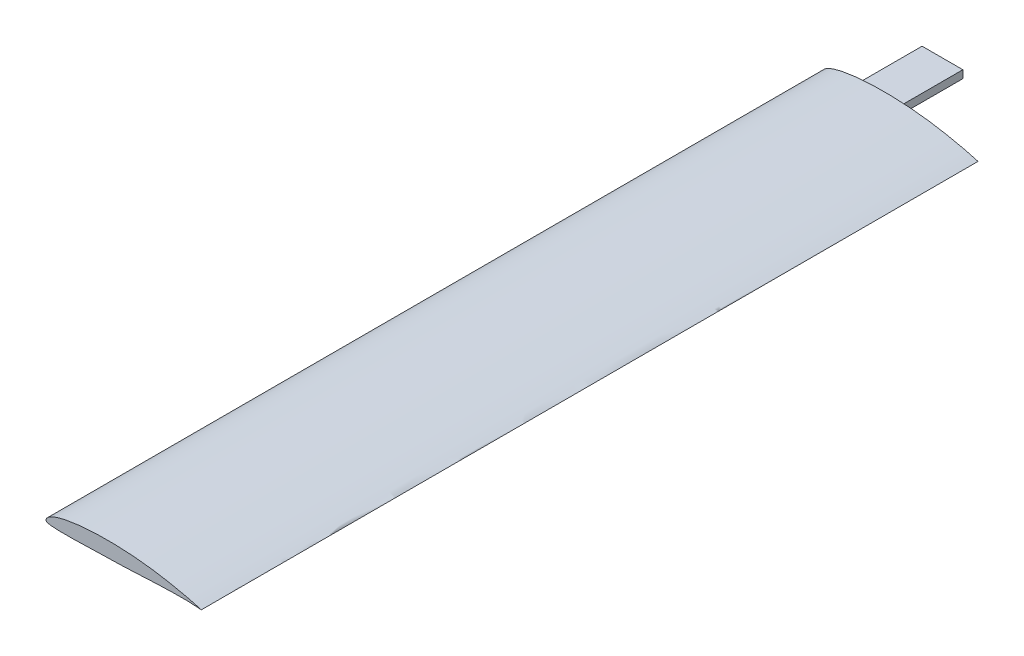
SolidWorks part; units mm, degrees
ref_plane "Front Plane" through (0, 0, 0) normal (0, 0, 1) x (1, 0, 0)
ref_plane "Top Plane" through (0, 0, 0) normal (0, 1, 0) x (1, 0, 0)
ref_plane "Right Plane" through (0, 0, 0) normal (1, 0, 0) x (0, 0, -1)
curve "Curve1"
  spline degree 3 poles (0.9957, 0.0006, 0) (1.0011, -0.0002, 0) (0.9959, 0.0009, 0) (0.992, 0.0022, 0) (0.9825, 0.005, 0) (0.9713, 0.0084, 0) (0.957, 0.0125, 0) (0.9402, 0.017, 0) (0.9208, 0.0217, 0) (0.8989, 0.0268, 0) (0.8748, 0.0321, 0) (0.8486, 0.0377, 0) (0.8205, 0.0435, 0) (0.7907, 0.0493, 0) (0.7596, 0.055, 0) (0.7273, 0.0605, 0) (0.6938, 0.0656, 0) (0.6594, 0.0702, 0) (0.6242, 0.0743, 0) (0.5883, 0.0778, 0) (0.552, 0.0808, 0) (0.5155, 0.0832, 0) (0.4788, 0.085, 0) (0.4423, 0.0861, 0) (0.4061, 0.0866, 0) (0.3705, 0.0865, 0) (0.3355, 0.0857, 0) (0.3015, 0.0843, 0) (0.2685, 0.0823, 0) (0.2368, 0.0797, 0) (0.2065, 0.0766, 0) (0.1779, 0.0729, 0) (0.151, 0.0687, 0) (0.126, 0.0641, 0) (0.1031, 0.059, 0) (0.0823, 0.0535, 0) (0.0638, 0.0477, 0) (0.0475, 0.0415, 0) (0.0337, 0.0351, 0) (0.0222, 0.0285, 0) (0.0131, 0.0217, 0) (0.0064, 0.0151, 0) (0.0018, 0.0085, 0) (0, 0.0023, 0) (-0.0004, -0.0036, 0) (0.0042, -0.0082, 0) (0.0115, -0.0108, 0) (0.0215, -0.0135, 0) (0.0347, -0.0154, 0) (0.0508, -0.0168, 0) (0.07, -0.0176, 0) (0.0921, -0.0181, 0) (0.117, -0.0183, 0) (0.1444, -0.0182, 0) (0.1743, -0.0179, 0) (0.2064, -0.0175, 0) (0.2404, -0.0168, 0) (0.2761, -0.016, 0) (0.3133, -0.0151, 0) (0.3517, -0.014, 0) (0.391, -0.0129, 0) (0.431, -0.0116, 0) (0.4715, -0.0102, 0) (0.5121, -0.0086, 0) (0.5527, -0.0067, 0) (0.5932, -0.0048, 0) (0.6332, -0.0027, 0) (0.6727, -0.0008, 0) (0.7112, 0.001, 0) (0.7485, 0.0026, 0) (0.7843, 0.0038, 0) (0.8183, 0.0047, 0) (0.8501, 0.0051, 0) (0.8795, 0.0053, 0) (0.9062, 0.005, 0) (0.9299, 0.0045, 0) (0.9504, 0.0037, 0) (0.9676, 0.0028, 0) (0.9807, 0.002, 0) (0.9914, 0.0009, 0) (0.9957, 0.0006, 0) (1.0011, -0.0002, 0) (0.9959, 0.0009, 0) knots -0.00876 -0.003931 -0.00099 0 0.000981 0.003818 0.008307 0.01426 0.021544 0.030087 0.039895 0.050943 0.063119 0.07632 0.090432 0.105336 0.120915 0.137032 0.153644 0.170716 0.188142 0.20585 0.223754 0.241763 0.259789 0.27774 0.295526 0.31306 0.33025 0.347009 0.363243 0.378876 0.393827 0.408018 0.421385 0.433867 0.445407 0.45597 0.465508 0.474013 0.481506 0.487961 0.493466 0.498109 0.501908 0.505061 0.50763 0.510153 0.5139 0.518982 0.525445 0.533392 0.54282 0.553698 0.565938 0.579453 0.594142 0.609906 0.626639 0.644212 0.662508 0.681404 0.700762 0.720455 0.740348 0.760327 0.780316 0.800229 0.819957 0.83938 0.858358 0.876742 0.89437 0.91109 0.926761 0.941228 0.954366 0.966044 0.976141 0.984569 0.99124 0.996069 0.99901 1 1.000981 1.003818 1.008307 periodic
sketch "Sketch1" plane through (0, 0, 0) normal (0, 0, 1) x (1, 0, 0)
  line L1 (20, 0) -> (0, 0) construction
  line L2 (0, 0) -> (0, 12.3044) construction
  spline S1 degree 3 poles (19.9149, 0.0124) (20.0212, -0.004) (19.9187, 0.0189) (19.8391, 0.0448) (19.6508, 0.0993) (19.4267, 0.1678) (19.1403, 0.251) (18.8046, 0.3407) (18.4164, 0.4352) (17.9794, 0.5368) (17.4964, 0.6443) (16.9719, 0.7563) (16.4102, 0.872) (15.8157, 0.9881) (15.1933, 1.1036) (14.5465, 1.2143) (13.8776, 1.3154) (13.1896, 1.4081) (12.4852, 1.4907) (11.7683, 1.5618) (11.0424, 1.6221) (10.3113, 1.6704) (9.5788, 1.7058) (8.8489, 1.7294) (8.1253, 1.7392) (7.412, 1.7372) (6.7128, 1.7222) (6.0317, 1.6945) (5.3723, 1.6553) (4.7384, 1.6044) (4.1334, 1.5416) (3.5605, 1.4687) (3.023, 1.385) (2.5236, 1.2926) (2.0648, 1.191) (1.6491, 1.0814) (1.278, 0.9656) (0.9535, 0.8423) (0.6763, 0.7145) (0.4465, 0.5831) (0.2651, 0.448) (0.1297, 0.315) (0.0387, 0.1832) (0.0013, 0.0598) (-0.0053, -0.0596) (0.0866, -0.1515) (0.2324, -0.2028) (0.4329, -0.258) (0.6956, -0.2955) (1.0182, -0.3229) (1.4017, -0.34) (1.8437, -0.3505) (2.3413, -0.3543) (2.8906, -0.3536) (3.4878, -0.3478) (4.1287, -0.3385) (4.8087, -0.3259) (5.523, -0.3103) (6.2667, -0.2922) (7.0346, -0.2716) (7.8214, -0.2493) (8.6216, -0.2246) (9.4303, -0.1968) (10.2427, -0.1648) (11.0553, -0.1288) (11.8644, -0.09) (12.6656, -0.0498) (13.4543, -0.0109) (14.2248, 0.0246) (14.9711, 0.0547) (15.687, 0.079) (16.3662, 0.0956) (17.0026, 0.1049) (17.5905, 0.1071) (18.124, 0.1018) (18.5984, 0.0911) (19.0074, 0.0755) (19.352, 0.0569) (19.6146, 0.0398) (19.8272, 0.0186) (19.9149, 0.0124) (20.0212, -0.004) (19.9187, 0.0189) knots -0.00876 -0.003931 -0.00099 0 0.000981 0.003818 0.008307 0.01426 0.021544 0.030087 0.039895 0.050943 0.063119 0.07632 0.090432 0.105336 0.120915 0.137032 0.153644 0.170716 0.188142 0.20585 0.223754 0.241763 0.259789 0.27774 0.295526 0.31306 0.33025 0.347009 0.363243 0.378876 0.393827 0.408018 0.421385 0.433867 0.445407 0.45597 0.465508 0.474013 0.481506 0.487961 0.493466 0.498109 0.501908 0.505061 0.50763 0.510153 0.5139 0.518982 0.525445 0.533392 0.54282 0.553698 0.565938 0.579453 0.594142 0.609906 0.626639 0.644212 0.662508 0.681404 0.700762 0.720455 0.740348 0.760327 0.780316 0.800229 0.819957 0.83938 0.858358 0.876742 0.89437 0.91109 0.926761 0.941228 0.954366 0.966044 0.976141 0.984569 0.99124 0.996069 0.99901 1 1.000981 1.003818 1.008307 only from (20, 0) to (20, 0)
  dimension "D1" = 20
extrude "Boss-Extrude1" add sketch "Sketch1" along normal blind 100
sketch "Sketch3" plane through (0, 0, 0) normal (0, 0, -1) x (-1, 0, 0)
  line L1 (-10.05, 0.25) -> (-4.8, 0.25)
  line L2 (-10.05, 0.25) -> (-10.05, 1.25)
  line L3 (-10.05, 1.25) -> (-4.8, 1.25)
  line L4 (-4.8, 0.25) -> (-4.8, 1.25)
  dimension "D1" = 1
  dimension "D2" = 5.25
  dimension "D3" = 4.8
  dimension "D4" = 1.25
extrude "Boss-Extrude2" add sketch "Sketch3" along normal blind 8
